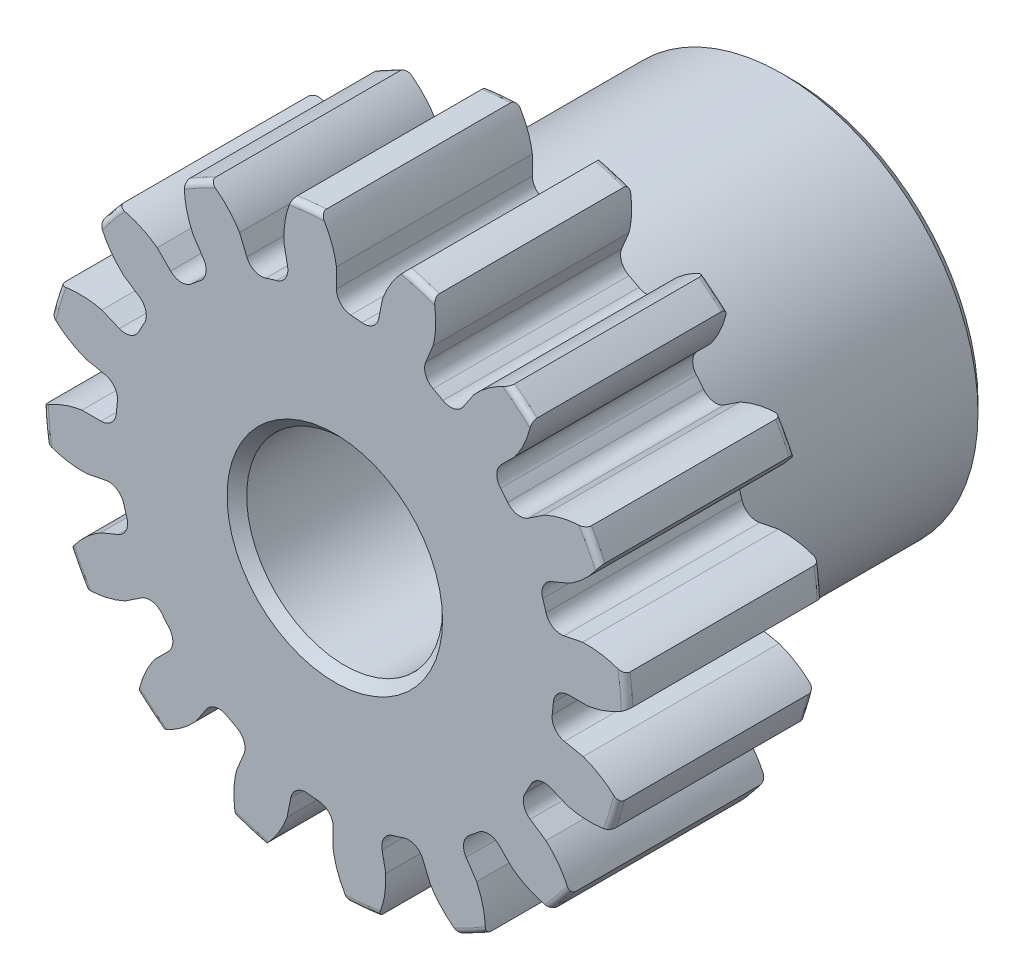
SolidWorks part; units mm, degrees
ref_plane "Front" through (0, 0, 0) normal (0, 0, 1) x (1, 0, 0)
ref_plane "Top" through (0, 0, 0) normal (0, 1, 0) x (1, 0, 0)
ref_plane "Right" through (0, 0, 0) normal (1, 0, 0) x (0, 0, -1)
sketch "Sketch1" plane through (0, 0, 0) normal (0, 0, 1) x (1, 0, 0)
  line L0 (-203.2, 0) -> (203.2, 0) construction
  circle A0 centre (0, 0) radius 7.112
  circle A1 centre (0, 0) radius 6.35 construction
  circle A3 centre (0, 0) radius 5.3261 construction
  dimension "D1" = 1.7859
  dimension "OD" = 14.224
  dimension "Ptich Dia" = 12.7
  dimension "Root Dia" = 10.6521
  dimension "D3" = 0.762
  dimension "Number of Teeth" = 406.4
extrude "Boss-Extrude1" add sketch "Sketch1" against normal blind 4.7625
sketch "Sketch2" plane through (0, 0, 0) normal (1, 0, 0) x (0, 0, -1)
  line L0 (4.7625, 0) -> (11.1125, 0)
  line L1 (4.7625, 0) -> (4.7625, 4.7625)
  line L2 (4.7625, 4.7625) -> (11.1125, 4.7625)
  line L3 (11.1125, 4.7625) -> (11.1125, 0)
  point P5 (11.1125, -4.7625)
  point P6 (0, -7.112)
  point P7 (4.7625, -7.112)
  point P9 (0, 7.112)
  dimension "Face Wd" = 4.7625
  dimension "B Hub Dia" = 9.525
  dimension "D O'all Lg." = 11.1125
revolve "Revolve1" add sketch "Sketch2" angle 360 about L0
fillet "Fillet2" radius 0.1422 3 edges at (7.112, 0, -4.7625) (7.112, 0, 0) (4.7625, 0, -4.7625)
sketch "Sketch3" plane through (0, 0, 0) normal (0, 0, 1) x (1, 0, 0)
  line L0 (0, 0) -> (0, 7.112) construction
  line L1 (-1.5393, 5.9519) -> (0, 6.35)
  line L2 (-9.5921, 6.35) -> (9.5921, 6.35) construction
  line L3 (-9.2865, 3.9483) -> (9.2865, 8.7517) construction
  line L4 (-1.5393, 5.9519) -> (0, 0) construction
  line L5 (-3.9262, 4.7307) -> (0, 0) construction
  line L6 (-3.9262, 4.7307) -> (-0.6424, 7.456) construction
  line L7 (-1.0733, 6.0533) -> (0, 0) construction
  line L8 (-1.0733, 6.0533) -> (0.0225, 6.2476) construction
  arc A0 (-1.5393, 5.9519) -> (-3.9262, 4.7307) centre (0, 0) ccw
  circle A1 centre (0, 0) radius 6.35 construction
  circle A2 centre (0, 0) radius 6.1477 construction
  arc A3 (-1.5393, 5.9519) -> (-1.0733, 6.0533) centre (0, 0) cw
  circle A4 centre (0, 0) radius 7.112 construction
  point P6 (0, 6.35)
  dimension "D1" = 1.5899
  dimension "Pressure Angle" = 14.5
  dimension "D2" = 2.7029
  dimension "D3" = 4.2674
  dimension "D4" = 0.477
  dimension "D5" = 1.1129
sketch "Sketch4" plane through (0, 0, 0) normal (0, 0, 1) x (1, 0, 0)
  line L0 (0, 0) -> (0.6194, 6.289) construction
  line L1 (0.0398, 6.1476) -> (0.0398, 5.3259)
  line L2 (0, 6.35) -> (1.2388, 6.228) construction
  line L3 (1.1603, 6.0372) -> (1, 5.2313)
  line L4 (0.0398, 5.3259) -> (0, 0) construction
  line L5 (0, 0) -> (0, 7.112) construction
  line L6 (-3.9262, 4.7307) -> (-0.6424, 7.456) construction
  line L7 (-3.9262, 4.7307) -> (-0.6424, 7.456) construction
  arc A0 (1, 5.2313) -> (0.0398, 5.3259) centre (0, 0) ccw
  arc A1 (0, 6.35) -> (1.2388, 6.228) centre (0, 0) cw construction
  circle A2 centre (0, 0) radius 6.35 construction
  circle A3 centre (0, 0) radius 6.1477 construction
  circle A4 centre (0, 0) radius 5.3261 construction
  arc A5 (2.0846, 7.1874) -> (-0.6424, 7.456) centre (0, 0) ccw
  spline S0 degree 2 poles (-0.6424, 7.456) (-0.0701, 6.8828) (0.0398, 6.1476) knots 0 0 0 1 1 1
  spline S1 degree 2 poles (2.0846, 7.1874) (1.4115, 6.7368) (1.1603, 6.0372) knots 0 0 0 1 1 1
  dimension "D1" = 1.2468
extrude "Cut-Extrude1" cut sketch "Sketch4" against normal through all
fillet "Fillet1" radius 0.374 2 edges at (1, 5.2313, -2.3813) (0.0398, 5.3259, -2.3813)
pattern_circular "CirPattern1" count 16 over 360 about axis through (0, 0, -4.7625) along (0, 0, 1) of "Cut-Extrude1", "Fillet1"
sketch "Sketch5" plane through (0, 0, 0) normal (0, 0, 1) x (1, 0, 0)
  circle A0 centre (0, 0) radius 2.3813
  circle A1 centre (0, 0) radius 1.5875 construction
  dimension "Bore Min" = 4.7625
  dimension "Bore Max" = 3.175
extrude "Cut-Extrude2" cut sketch "Sketch5" against normal through all
chamfer "Chamfer1" distance 0.2381 angle 45 3 edges at (4.7625, 0, -11.1125) (2.3813, 0, 0) (2.3813, 0, -11.1125)
sketch "Pitch Dia" plane through (0, 0, 0) normal (0, 0, 1) x (1, 0, 0)
  circle A0 centre (0, 0) radius 6.35 construction
  circle A1 centre (0, 0) radius 6.35 construction
equation "\"D1@Boss-Extrude1\" = \"Face Wd@Sketch2\""
equation "\"D2@Sketch3\" = \"D1@Sketch3\"*1.7"
equation "\"D3@Sketch3\" = \"D1@Sketch3\"+\"D2@Sketch3\"-.001"
equation "\"D4@Sketch3\" = \"D1@Sketch3\"*.3"
equation "\"D5@Sketch3\" = \"D1@Sketch3\"-\"D4@Sketch3\""
equation "\"D1@Sketch4\" = 1.5708/(\"Number of Teeth@Sketch1\"/\"Ptich Dia@Sketch1\")"
equation "\"D1@Chamfer1\" = \"B Hub Dia@Sketch2\"*.025"
equation "\"D1@CirPattern1\" = \"Number of Teeth@Sketch1\""
equation "\"D1@Fillet1\" = \"D1@Sketch4\"*.3"
equation "\"D1@Fillet2\" = \"OD@Sketch1\"*.01"
equation "\"D1@Sketch1\" = 2.250/(\"Number of Teeth@Sketch1\"/\"Ptich Dia@Sketch1\")"
